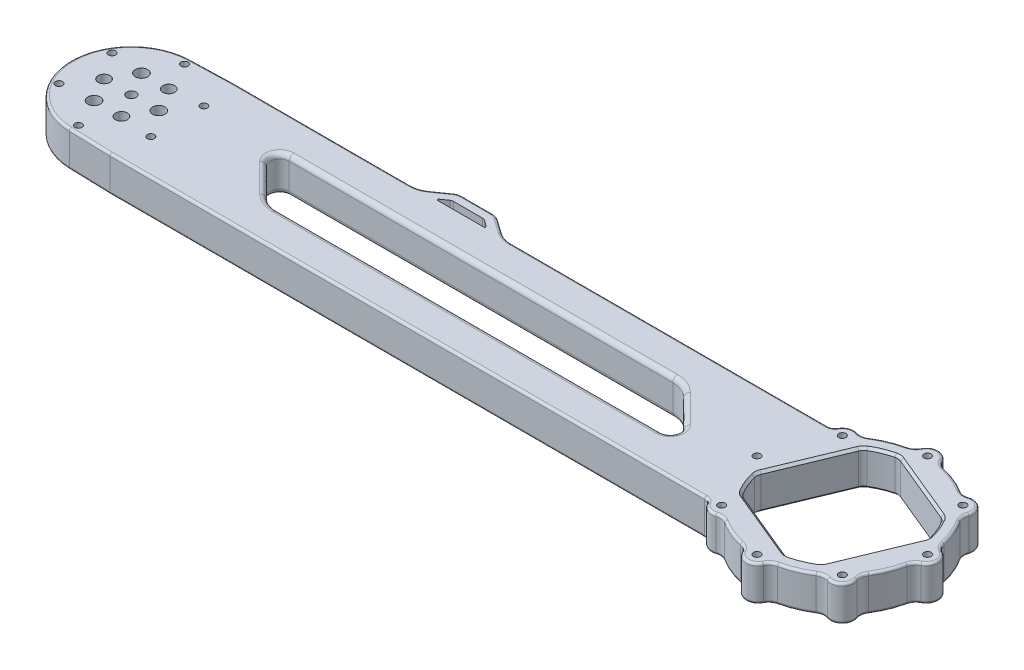
SolidWorks part; units mm, degrees
ref_plane "前视基准面" through (0, 0, 0) normal (0, 0, 1) x (1, 0, 0)
ref_plane "上视基准面" through (0, 0, 0) normal (0, 1, 0) x (1, 0, 0)
ref_plane "右视基准面" through (0, 0, 0) normal (1, 0, 0) x (0, 0, -1)
sketch "草图1" plane through (0, 0, 0) normal (0, 1, 0) x (1, 0, 0)
  line L0 (300, 0) -> (0, 0) construction
  line L1 (16.8819, 26) -> (255.487, 26)
  line L2 (16.8819, -26) -> (255.487, -26)
  line L3 (16.8819, 26) -> (-0.7388, 25.4893)
  line L4 (16.8819, -26) -> (-0.7388, -25.4893)
  line L5 (300, 42.2133) -> (300, -42.2133) construction
  line L6 (0, 22.375) -> (-19.3773, 11.1875) construction
  line L7 (-19.3773, 11.1875) -> (-19.3773, -11.1875) construction
  line L8 (-19.3773, -11.1875) -> (0, -22.375) construction
  line L9 (0, -22.375) -> (19.3773, -11.1875) construction
  line L10 (19.3773, -11.1875) -> (19.3773, 11.1875) construction
  line L11 (19.3773, 11.1875) -> (0, 22.375) construction
  line L12 (268.5656, 26.0225) -> (259.3718, 3.8268) construction
  line L13 (259.3718, -3.8268) -> (268.5656, -26.0225) construction
  line L14 (273.9775, -31.4344) -> (296.1732, -40.6282) construction
  line L15 (303.8268, -40.6282) -> (326.0225, -31.4344)
  line L16 (331.4344, -26.0225) -> (340.6282, -3.8268)
  line L17 (340.6282, 3.8268) -> (331.4344, 26.0225)
  line L18 (326.0225, 31.4344) -> (303.8268, 40.6282)
  line L19 (296.1732, 40.6282) -> (273.9775, 31.4344) construction
  line L20 (296.1732, 40.6282) -> (265.8195, 28.0553)
  line L21 (296.1732, -40.6282) -> (265.8195, -28.0553)
  line L22 (286.3077, 33.056) -> (333.056, 13.6923) construction
  line L23 (300, -36) -> (325.4558, -25.4558) construction
  line L24 (325.4558, -25.4558) -> (336, 0) construction
  line L25 (336, 0) -> (325.4558, 25.4558) construction
  line L26 (325.4558, 25.4558) -> (300, 36) construction
  line L27 (300, 36) -> (274.5442, 25.4558) construction
  line L28 (274.5442, 25.4558) -> (264, 0) construction
  line L29 (264, 0) -> (274.5442, -25.4558) construction
  line L30 (274.5442, -25.4558) -> (300, -36) construction
  line L31 (286.3077, 33.056) -> (266.944, -13.6923) construction
  line L32 (333.056, 13.6923) -> (313.6923, -33.056) construction
  line L33 (266.944, -13.6923) -> (313.6923, -33.056) construction
  line L34 (286.3077, 33.056) -> (313.6923, -33.056) construction
  line L35 (333.056, 13.6923) -> (266.944, -13.6923) construction
  line L36 (295.1162, 29.4075) -> (324.2476, 17.3408)
  line L37 (282.6592, 24.2476) -> (270.5925, -4.8838)
  line L38 (275.7524, -17.3408) -> (304.8838, -29.4075)
  line L39 (329.4075, 4.8838) -> (317.3408, -24.2476)
  circle A0 centre (0, 0) radius 25.5 construction
  circle A1 centre (300, 0) radius 39 construction
  arc A2 (-0.7388, 25.4893) -> (-0.7388, -25.4893) centre (0, 0) ccw
  circle A3 centre (0, 0) radius 2
  circle A4 centre (0, 0) radius 22.375 construction
  circle A5 centre (0, 0) radius 19.3773 construction
  circle A6 centre (0, 22.375) radius 1.5
  circle A7 centre (19.3773, 11.1875) radius 1.5
  circle A8 centre (19.3773, -11.1875) radius 1.5
  circle A9 centre (0, -22.375) radius 1.5
  circle A10 centre (-19.3773, -11.1875) radius 1.5
  circle A11 centre (-19.3773, 11.1875) radius 1.5
  circle A12 centre (300, 0) radius 39 construction
  arc A13 (268.5656, 26.0225) -> (273.9775, 31.4344) centre (277.8044, 22.1956) cw construction
  arc A14 (259.3718, 3.8268) -> (259.3718, -3.8268) centre (268.6106, 0) ccw construction
  arc A15 (268.5656, -26.0225) -> (273.9775, -31.4344) centre (277.8044, -22.1956) ccw construction
  arc A16 (296.1732, -40.6282) -> (303.8268, -40.6282) centre (300, -31.3894) ccw
  arc A17 (326.0225, -31.4344) -> (331.4344, -26.0225) centre (322.1956, -22.1956) ccw
  arc A18 (340.6282, -3.8268) -> (340.6282, 3.8268) centre (331.3894, 0) ccw
  arc A19 (331.4344, 26.0225) -> (326.0225, 31.4344) centre (322.1956, 22.1956) ccw
  arc A20 (303.8268, 40.6282) -> (296.1732, 40.6282) centre (300, 31.3894) ccw
  arc A21 (255.487, -26) -> (265.8195, -28.0553) centre (255.487, -53) cw
  arc A22 (255.487, 26) -> (265.8195, 28.0553) centre (255.487, 53) ccw
  circle A23 centre (300, 0) radius 36 construction
  circle A25 centre (300, 36) radius 3 construction
  circle A26 centre (300, 36) radius 1.5
  circle A27 centre (325.4558, 25.4558) radius 1.5
  circle A28 centre (336, 0) radius 1.5
  circle A29 centre (325.4558, -25.4558) radius 1.5
  circle A30 centre (300, -36) radius 1.5
  circle A31 centre (274.5442, -25.4558) radius 1.5
  circle A32 centre (264, 0) radius 1.5
  circle A33 centre (274.5442, 25.4558) radius 1.5
  circle A35 centre (300, 0) radius 30.5 construction
  arc A36 (292.6172, 29.593) -> (284.295, 26.1458) centre (300, 0) ccw
  arc A37 (326.1458, 15.705) -> (329.593, 7.3828) centre (300, 0) cw
  arc A38 (315.705, -26.1458) -> (307.3828, -29.593) centre (300, 0) cw
  arc A39 (270.407, -7.3828) -> (273.8542, -15.705) centre (300, 0) ccw
  arc A40 (270.407, -7.3828) -> (270.5925, -4.8838) centre (274.2881, -6.4145) cw
  arc A41 (273.8542, -15.705) -> (275.7524, -17.3408) centre (277.2832, -13.6453) ccw
  arc A42 (307.3828, -29.593) -> (304.8838, -29.4075) centre (306.4145, -25.7119) cw
  arc A43 (315.705, -26.1458) -> (317.3408, -24.2476) centre (313.6453, -22.7168) ccw
  arc A44 (329.593, 7.3828) -> (329.4075, 4.8838) centre (325.7119, 6.4145) cw
  arc A45 (326.1458, 15.705) -> (324.2476, 17.3408) centre (322.7168, 13.6453) ccw
  arc A46 (292.6172, 29.593) -> (295.1162, 29.4075) centre (293.5855, 25.7119) cw
  arc A47 (284.295, 26.1458) -> (282.6592, 24.2476) centre (286.3547, 22.7168) ccw
  point P30 (260.8576, -26)
  point P60 (260.8576, 26)
  point P98 (270.1072, -6.0556)
  point P101 (274.5807, -16.8555)
  point P104 (306.0556, -29.8928)
  point P107 (316.8555, -25.4193)
  point P110 (329.8928, 6.0556)
  point P113 (325.4193, 16.8555)
  point P116 (293.9444, 29.8928)
  point P119 (283.1445, 25.4193)
  dimension "D1" = 51
  dimension "D2" = 78
  dimension "D6" = 4
  dimension "D7" = 44.75
  dimension "D8" = 3
  dimension "D9" = 10
  dimension "D10" = 27
  dimension "D11" = 6
  dimension "D12" = 72
  dimension "D13" = 3
  dimension "D14" = 61
  dimension "D16" = 4
  dimension "D3" = 300
  dimension "D4" = 52
  dimension "D5" = 31
  dimension "D15" = 25.3
extrude "凸台-拉伸1" add sketch "草图1" along normal blind 15
sketch "草图2" plane through (0, 15, 0) normal (0, 1, 0) x (1, 0, 0)
  line L0 (300, 36) -> (300, 35.5) construction
  line L1 (255.487, 26) -> (269.979, 26)
  line L2 (255.487, 26) -> (16.8819, 26) construction
  line L3 (255.487, -26) -> (269.979, -26)
  line L4 (16.8819, -26) -> (255.487, -26) construction
  line L5 (255.487, 26) -> (255.487, 57.0764)
  line L6 (255.487, 57.0764) -> (351.5997, 57.0764)
  line L7 (351.5997, 57.0764) -> (351.5997, -49.8411)
  line L8 (351.5997, -49.8411) -> (255.487, -49.8411)
  line L9 (255.487, -49.8411) -> (255.487, -26)
  line L10 (72.5, 0) -> (217.5, 0) construction
  line L11 (72.5, 11) -> (217.5, 11)
  line L12 (72.5, -11) -> (217.5, -11)
  circle A0 centre (300, 0) radius 36 construction
  arc A1 (295.0023, 35.6514) -> (304.9977, 35.6514) centre (300, 35.5) cw
  arc A2 (304.9977, 35.6514) -> (321.6754, 28.7433) centre (300, 0) cw
  arc A3 (72.5, 11) -> (72.5, -11) centre (72.5, 0) ccw
  arc A4 (321.6754, 28.7433) -> (328.7433, 21.6754) centre (325.1023, 25.1023) cw
  arc A5 (335.6514, 4.9977) -> (335.6514, -4.9977) centre (335.5, 0) cw
  arc A6 (328.7433, -21.6754) -> (321.6754, -28.7433) centre (325.1023, -25.1023) cw
  arc A7 (304.9977, -35.6514) -> (295.0023, -35.6514) centre (300, -35.5) cw
  arc A8 (278.3246, -28.7433) -> (271.2567, -21.6754) centre (274.8977, -25.1023) cw construction
  arc A9 (264.3486, -4.9977) -> (264.3486, 4.9977) centre (264.5, 0) cw construction
  arc A10 (271.2567, 21.6754) -> (278.3246, 28.7433) centre (274.8977, 25.1023) cw construction
  arc A11 (328.7433, 21.6754) -> (335.6514, 4.9977) centre (300, 0) cw
  arc A12 (335.6514, -4.9977) -> (328.7433, -21.6754) centre (300, 0) cw
  arc A13 (321.6754, -28.7433) -> (304.9977, -35.6514) centre (300, 0) cw
  arc A14 (295.0023, -35.6514) -> (278.3246, -28.7433) centre (300, 0) cw
  arc A15 (271.2567, -21.6754) -> (264.3486, -4.9977) centre (300, 0) cw construction
  arc A16 (264.3486, 4.9977) -> (271.2567, 21.6754) centre (300, 0) cw construction
  arc A17 (278.3246, 28.7433) -> (295.0023, 35.6514) centre (300, 0) cw
  arc A18 (265.8195, -28.0553) -> (255.487, -26) centre (255.487, -53) ccw construction
  arc A19 (269.979, 26) -> (278.3246, 28.7433) centre (274.8977, 25.1023) cw
  arc A20 (269.979, -26) -> (278.3246, -28.7433) centre (274.8977, -25.1023) ccw
  arc A21 (217.5, -11) -> (217.5, 11) centre (217.5, 0) ccw
  point P3 (274.5442, 25.4558)
  point P6 (300, -36)
  point P14 (300, 36)
  point P39 (300, 0)
  point P52 (300, 0)
  point P56 (145, 0)
  dimension "D1" = 5
  dimension "D3" = 0.5
  dimension "D5" = 15
  dimension "D6" = 145
  dimension "D7" = 145
  dimension "D2" = 8
  dimension "D4" = 8
extrude "切除-拉伸1" cut sketch "草图2" against normal through all both and the other way through all
fillet "圆角1" radius 5 12 edges at (278.3246, 7.5, 28.7433) (295.0023, 7.5, 35.6514) (304.9977, 7.5, 35.6514) (321.6754, 7.5, 28.7433) (328.7433, 7.5, 21.6754) (335.6514, 7.5, 4.9977) (335.6514, 7.5, -4.9977) (328.7433, 7.5, -21.6754) (321.6754, 7.5, -28.7433) (304.9977, 7.5, -35.6514) (295.0023, 7.5, -35.6514) (278.3246, 7.5, -28.7433)
fillet "圆角3" radius 3 2 edges at (269.979, 7.5, 26) (269.979, 7.5, -26)
sketch "草图4" plane through (0, 15, 0) normal (0, 1, 0) x (1, 0, 0)
  circle A0 centre (5.7735, -10) radius 2.5 construction
  circle A1 centre (-5.7735, -10) radius 2.65 construction
  circle A2 centre (-11.547, 0) radius 2.5 construction
  circle A3 centre (11.547, 0) radius 2.65 construction
  circle A4 centre (5.7735, 10) radius 2.5 construction
  circle A5 centre (-5.7735, 10) radius 2.65 construction
  circle A6 centre (5.7735, -10) radius 2.5
  circle A7 centre (-5.7735, -10) radius 2.65
  circle A8 centre (-11.547, 0) radius 2.5
  circle A9 centre (11.547, 0) radius 2.65
  circle A10 centre (5.7735, 10) radius 2.5
  circle A11 centre (-5.7735, 10) radius 2.65
extrude "切除-拉伸2" cut sketch "草图4" against normal through all both and the other way through all
sketch "草图5" plane through (0, 15, 0) normal (0, 1, 0) x (1, 0, 0)
  line L0 (119.4494, 33) -> (106.5693, 33)
  line L1 (267.9114, 26) -> (16.8819, 26) construction
  line L2 (103.7014, 32.0958) -> (94.9957, 26)
  line L3 (94.9957, 26) -> (94.9957, 20.525)
  line L4 (94.9957, 20.525) -> (131.0229, 20.525)
  line L5 (131.0229, 20.525) -> (131.0229, 26)
  line L6 (131.0229, 26) -> (122.3173, 32.0958)
  line L7 (126.1557, 24.525) -> (119.7647, 29) construction
  line L8 (119.1341, 29) -> (106.8846, 29)
  line L9 (106.254, 29) -> (99.863, 24.525) construction
  line L10 (99.863, 24.525) -> (99.863, 24.525)
  line L12 (126.1557, 24.525) -> (126.1557, 24.525)
  line L13 (99.863, 24.525) -> (126.1557, 24.525) construction
  line L14 (122.7805, 26) -> (103.2382, 26)
  line L15 (123.0099, 26.7277) -> (120.2812, 28.6383)
  line L16 (105.7374, 28.6383) -> (103.0087, 26.7277)
  line L17 (119.7647, 29) -> (106.254, 29) construction
  line L18 (121.0259, 33) -> (104.9928, 33) construction
  line L19 (104.9928, 33) -> (94.9957, 26) construction
  line L20 (131.0229, 26) -> (121.0259, 33) construction
  arc A0 (106.8846, 29) -> (105.7374, 28.6383) centre (106.8846, 27) ccw
  arc A1 (120.2812, 28.6383) -> (119.1341, 29) centre (119.1341, 27) ccw
  arc A2 (103.2382, 26) -> (103.0087, 26.7277) centre (103.2382, 26.4) cw
  arc A3 (122.7805, 26) -> (123.0099, 26.7277) centre (122.7805, 26.4) ccw
  arc A4 (106.5693, 33) -> (103.7014, 32.0958) centre (106.5693, 28) ccw
  arc A5 (119.4494, 33) -> (122.3173, 32.0958) centre (119.4494, 28) cw
  point P24 (101.9695, 26)
  point P27 (124.0491, 26)
  dimension "D4" = 2
  dimension "D5" = 0.4
  dimension "D6" = 5
  dimension "D1" = 7
  dimension "D2" = 145
  dimension "D3" = 4
extrude "凸台-拉伸2" add sketch "草图5" against normal up to surface (15 mm away) contours A5 L0 A4 L2 L3 L4 L5 L6 A3 L14 A2 L16 A0 L8 A1 L15 up to face at (-5.7735, 0, 12.65)
sketch "草图6" plane through (0, 15, 0) normal (0, 1, 0) x (1, 0, 0)
  line L0 (64.7218, -7.7782) -> (52.7721, 4.1716)
  line L1 (72.5, 11) -> (55.6005, 11)
  line L2 (217.5, 11) -> (72.5, 11) construction
  line L3 (225.2782, 7.7782) -> (237.2279, -4.1716)
  line L4 (234.3995, -11) -> (217.5, -11)
  arc A0 (72.5, 11) -> (72.5, -11) centre (72.5, 0) ccw construction
  arc A1 (64.7218, -7.7782) -> (72.5, 11) centre (72.5, 0) cw
  arc A2 (52.7721, 4.1716) -> (55.6005, 11) centre (55.6005, 7) cw
  arc A3 (217.5, -11) -> (217.5, 11) centre (217.5, 0) ccw construction
  arc A4 (237.2279, -4.1716) -> (234.3995, -11) centre (234.3995, -7) cw
  arc A5 (217.5, -11) -> (225.2782, 7.7782) centre (217.5, 0) ccw
  dimension "D2" = 4
  dimension "D3" = 4
  dimension "D1" = 45
extrude "切除-拉伸3" cut sketch "草图6" against normal through all
fillet "圆角6" radius 10 2 edges at (131.0229, 7.5, -26) (94.9957, 7.5, -26)
fillet "圆角4" radius 1 80 edges at (8.0716, 15, -25.7446) (8.0716, 15, 25.7446) (8.0716, 0, -25.7446) (8.0716, 0, 25.7446) (142.3967, 0, 26) (269.4305, 0, 26.413) (273.0774, 0, 29.7592) (278.6335, 0, 29.6439) (286.2234, 0, 33.2597) (294.147, 0, 36.0698) (300, 0, 40.5) (305.853, 0, 36.0698) (313.7766, 0, 33.2597) (321.3665, 0, 29.6439) (328.6378, 0, 28.6378) (329.6439, 0, 21.3665) (333.2597, 0, 13.7766) (336.0698, 0, 5.853) (340.5, 0, 0) (336.0698, 0, -5.853) (333.2597, 0, -13.7766) (329.6439, 0, -21.3665) (328.6378, 0, -28.6378) (321.3665, 0, -29.6439) (313.7766, 0, -33.2597) (305.853, 0, -36.0698) (300, 0, -40.5) (294.147, 0, -36.0698) (286.2234, 0, -33.2597) (278.6335, 0, -29.6439) (273.0774, 0, -29.7592) (269.4305, 0, -26.413) (142.3967, 15, 26) (269.4305, 15, 26.413) (273.0774, 15, 29.7592) (278.6335, 15, 29.6439) (286.2234, 15, 33.2597) (294.147, 15, 36.0698) (300, 15, 40.5) (305.853, 15, 36.0698) (313.7766, 15, 33.2597) (321.3665, 15, 29.6439) (328.6378, 15, 28.6378) (329.6439, 15, 21.3665) (333.2597, 15, 13.7766) (336.0698, 15, 5.853) (340.5, 15, 0) (336.0698, 15, -5.853) (333.2597, 15, -13.7766) (329.6439, 15, -21.3665) (328.6378, 15, -28.6378) (321.3665, 15, -29.6439) (313.7766, 15, -33.2597) (305.853, 15, -36.0698) (300, 15, -40.5) (294.147, 15, -36.0698) (286.2234, 15, -33.2597) (278.6335, 15, -29.6439) (273.0774, 15, -29.7592) (269.4305, 15, -26.413) (-25.5, 15, 0) (-25.5, 0, 0) (201.0437, 0, -26) (54.3623, 0, -26) (201.0437, 15, -26) (54.3623, 15, -26) (94.8498, 0, -26.4628) (100.64, 0, -29.9521) (100.64, 15, -29.9521) (105.0657, 0, -32.7686) (105.0657, 15, -32.7686) (113.0093, 0, -33) (113.0093, 15, -33) (120.9529, 0, -32.7686) (120.9529, 15, -32.7686) (125.3787, 15, -29.9521) (125.3787, 0, -29.9521) (131.1688, 0, -26.4628) (94.8498, 15, -26.4628) (131.1688, 15, -26.4628)
fillet "圆角5" radius 2 16 edges at (68.2905, 0, 10.1627) (136.5503, 0, -11) (221.7095, 0, -10.1627) (68.2905, 15, 10.1627) (136.5503, 15, -11) (221.7095, 15, -10.1627) (153.4497, 0, 11) (153.4497, 15, 11) (58.747, 0, 1.8033) (51.905, 0, -8.5307) (231.253, 0, -1.8033) (238.095, 0, 8.5307) (58.747, 15, 1.8033) (51.905, 15, -8.5307) (231.253, 15, -1.8033) (238.095, 15, 8.5307)
chamfer "倒角1" distance 1 angle 45 32 edges at (290.3181, 0, 23.3742) (306.1184, 0, 29.701) (274.6719, 0, 16.6754) (311.6718, 0, 28.1783) (271.8217, 0, 11.6718) (316.6754, 0, 25.3281) (270.299, 0, 6.1184) (323.3742, 0, 9.6819) (276.6258, 0, -9.6819) (329.701, 0, -6.1184) (283.3246, 0, -25.3281) (328.1783, 0, -11.6718) (288.3282, 0, -28.1783) (325.3281, 0, -16.6754) (293.8816, 0, -29.701) (309.6819, 0, -23.3742) (290.3181, 15, 23.3742) (306.1184, 15, 29.701) (274.6719, 15, 16.6754) (311.6718, 15, 28.1783) (271.8217, 15, 11.6718) (316.6754, 15, 25.3281) (270.299, 15, 6.1184) (323.3742, 15, 9.6819) (276.6258, 15, -9.6819) (329.701, 15, -6.1184) (283.3246, 15, -25.3281) (328.1783, 15, -11.6718) (288.3282, 15, -28.1783) (325.3281, 15, -16.6754) (293.8816, 15, -29.701) (309.6819, 15, -23.3742)
